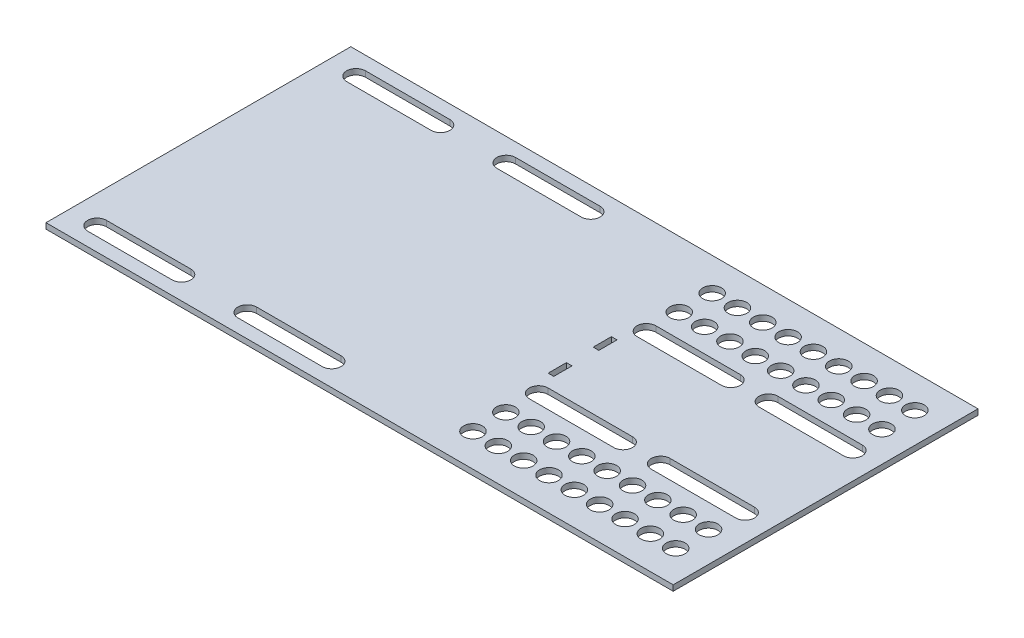
SolidWorks part; units mm, degrees
material "Balsa"
ref_plane "Front Plane" through (0, 0, 0) normal (0, 0, 1) x (1, 0, 0)
ref_plane "Top Plane" through (0, 0, 0) normal (0, 1, 0) x (1, 0, 0)
ref_plane "Right Plane" through (0, 0, 0) normal (1, 0, 0) x (0, 0, -1)
sketch "Sketch1" plane through (0, 0, 0) normal (0, 1, 0) x (1, 0, 0)
  line L1 (0, 0) -> (334.17, 0)
  line L2 (0, 0) -> (0, -162.4)
  line L3 (0, -162.4) -> (334.17, -162.4)
  line L4 (334.17, 0) -> (334.17, -162.4)
  dimension "D1" = 162.4
  dimension "D2" = 334.17
extrude "Boss-Extrude1" add sketch "Sketch1" along normal blind 3
sketch "Sketch2" plane through (0, 0, 0) normal (0, 1, 0) x (1, 0, 0)
  line L0 (210, -52.5) -> (255, -52.5) construction
  line L1 (210, -47.5) -> (255, -47.5)
  line L2 (210, -57.5) -> (255, -57.5)
  line L3 (334.17, 0) -> (0, 0) construction
  line L4 (0, 0) -> (0, -162.4) construction
  line L5 (334.17, -162.4) -> (334.17, 0) construction
  line L6 (0, -81.2) -> (334.17, -81.2) construction
  line L7 (275, -57.5) -> (320, -57.5)
  line L8 (275, -47.5) -> (320, -47.5)
  line L9 (275, -52.5) -> (320, -52.5) construction
  line L11 (15, -17.2) -> (60, -17.2)
  line L12 (15, -7.2) -> (60, -7.2)
  line L13 (15, -12.2) -> (60, -12.2) construction
  line L14 (0, 0) -> (0, -162.4) construction
  line L15 (95, -12.2) -> (140, -12.2) construction
  line L16 (95, -7.2) -> (140, -7.2)
  line L17 (95, -17.2) -> (140, -17.2)
  arc A0 (210, -47.5) -> (210, -57.5) centre (210, -52.5) ccw
  arc A1 (255, -57.5) -> (255, -47.5) centre (255, -52.5) ccw
  circle A4 centre (210, -17.5) radius 5
  circle A5 centre (223.5, -17.5) radius 5
  circle A6 centre (237, -17.5) radius 5
  circle A7 centre (250.5, -17.5) radius 5
  circle A8 centre (264, -17.5) radius 5
  circle A9 centre (277.5, -17.5) radius 5
  circle A10 centre (291, -17.5) radius 5
  circle A11 centre (304.5, -17.5) radius 5
  circle A15 centre (223.5, -35) radius 5
  circle A16 centre (237, -35) radius 5
  circle A17 centre (250.5, -35) radius 5
  circle A18 centre (264, -35) radius 5
  circle A19 centre (277.5, -35) radius 5
  circle A20 centre (291, -35) radius 5
  circle A21 centre (304.5, -35) radius 5
  circle A25 centre (210, -35) radius 5
  arc A64 (275, -47.5) -> (275, -57.5) centre (275, -52.5) ccw
  arc A65 (320, -57.5) -> (320, -47.5) centre (320, -52.5) ccw
  arc A66 (15, -7.2) -> (15, -17.2) centre (15, -12.2) ccw
  arc A67 (60, -17.2) -> (60, -7.2) centre (60, -12.2) ccw
  arc A68 (95, -7.2) -> (95, -17.2) centre (95, -12.2) ccw
  arc A69 (140, -17.2) -> (140, -7.2) centre (140, -12.2) ccw
  circle A72 centre (318, -17.5) radius 5
  circle A73 centre (318, -35) radius 5
  point P2 (232.5, -52.5)
  point P17 (37.5, -12.2)
  point P26 (297.5, -52.5)
  point P64 (117.5, -12.2)
  dimension "D2" = 5
  dimension "D5" = 10
  dimension "D15" = 5
  dimension "D1" = 47.5
  dimension "D3" = 210
  dimension "D6" = 17.5
  dimension "D4" = 13.5
  dimension "D9" = 45
  dimension "D11" = 65
  dimension "D12" = 35
  dimension "D13" = 64
  dimension "D14" = 45
  dimension "D16" = 15
  dimension "D18" = 80
  dimension "D7" = 9
  dimension "D8" = 2
  dimension "D10" = 2
  dimension "D17" = 2
extrude "Cut-Extrude1" cut sketch "Sketch2" along normal blind 17
ref_plane "Plane1" through (0, 0, 81.2) normal (0, 0, 1) x (1, 0, 0)
mirror "Mirror1" about plane through (0, 0, 81.2) normal (0, 0, 1) of "Cut-Extrude1"
sketch "Sketch3" plane through (0, 0, 0) normal (0, 1, 0) x (1, 0, 0)
  line L1 (203.2, -64.35) -> (206.2, -64.35)
  line L2 (203.2, -64.35) -> (203.2, -74.05)
  line L3 (203.2, -74.05) -> (206.2, -74.05)
  line L4 (206.2, -64.35) -> (206.2, -74.05)
  line L5 (203.2, -64.35) -> (206.2, -74.05) construction
  line L6 (203.2, -74.05) -> (206.2, -64.35) construction
  line L7 (203.2, -88.35) -> (206.2, -88.35)
  line L8 (203.2, -88.35) -> (203.2, -98.05)
  line L9 (203.2, -98.05) -> (206.2, -98.05)
  line L10 (206.2, -88.35) -> (206.2, -98.05)
  line L11 (203.2, -88.35) -> (206.2, -98.05) construction
  line L12 (203.2, -98.05) -> (206.2, -88.35) construction
  line L13 (0, 0) -> (0, -162.4) construction
  line L14 (0, -81.2) -> (334.17, -81.2) construction
  line L15 (334.17, -162.4) -> (334.17, 0) construction
  point P0 (204.7, -69.2)
  point P5 (204.7, -93.2)
  dimension "D2" = 9.7
  dimension "D3" = 3
  dimension "D4" = 9.7
  dimension "D5" = 3
  dimension "D1" = 203.2
  dimension "D7" = 12
  dimension "D6" = 12
extrude "Cut-Extrude3" cut sketch "Sketch3" along normal blind 45
equation "\"Length\"= 334.17"
equation "\"D2@Sketch1\"=\"Length\""
equation "\"Width\"= 152.4 + 10"
equation "\"D1@Sketch1\"=\"Width\""
equation "\"D7@Sketch2\"=((\"Length\"-\"D3@Sketch2\")/\"D4@Sketch2\")"
equation "\"D10@Sketch2\"=(\"Length\"-2*\"D3@Sketch2\")/\"D11@Sketch2\""
equation "\"D12@Sketch2\"=\"D6@Sketch2\"+17.5"
equation "\"D1@Sketch2\"=\"D12@Sketch2\"+12.5"
equation "\"D6@Sketch3\"=\"D7@Sketch3\""
